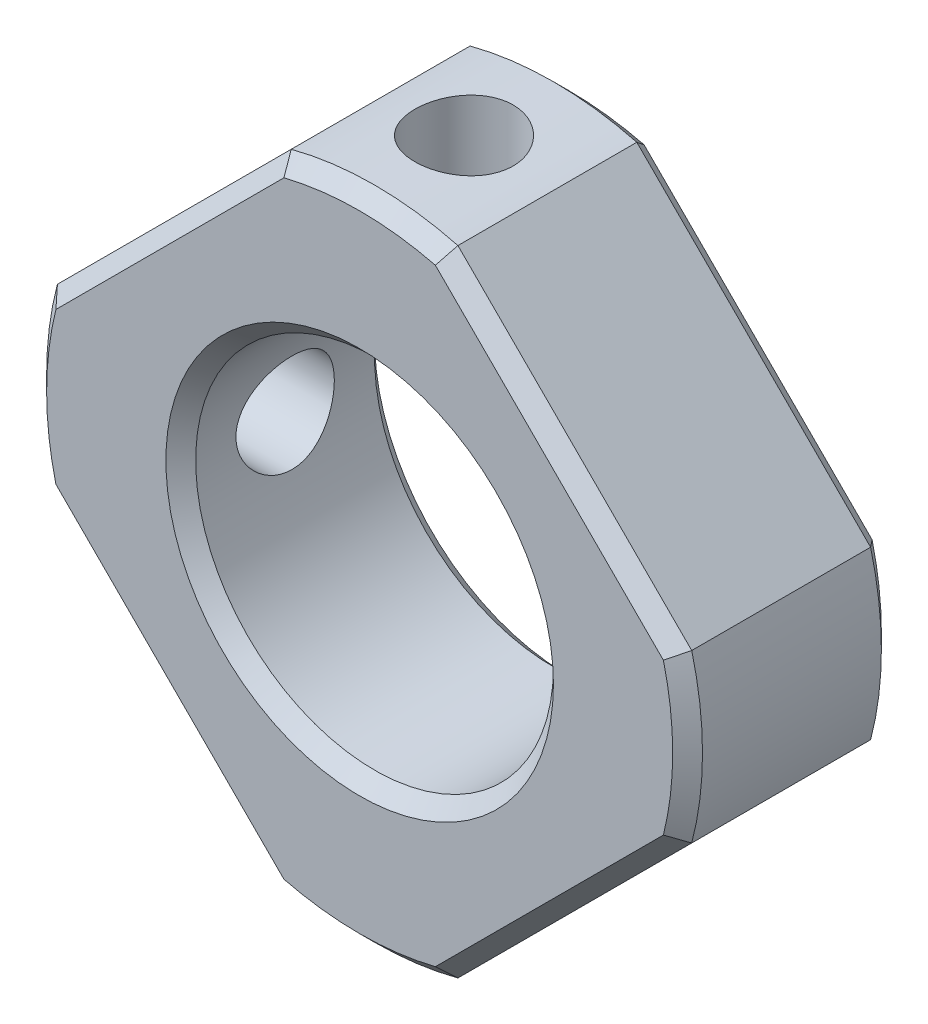
SolidWorks part; units mm, degrees
ref_plane "Front Plane" through (0, 0, 0) normal (0, 0, 1) x (1, 0, 0)
ref_plane "Top Plane" through (0, 0, 0) normal (0, 1, 0) x (1, 0, 0)
ref_plane "Right Plane" through (0, 0, 0) normal (1, 0, 0) x (0, 0, -1)
sketch "Sketch1" plane through (0, 0, 0) normal (0, 0, 1) x (1, 0, 0)
  line L1 (0, -13.435) -> (-13.435, 0)
  line L2 (0, -13.435) -> (13.435, 0)
  line L3 (13.435, 0) -> (0, 13.435)
  line L4 (-13.435, 0) -> (0, 13.435)
  line L5 (0, -13.435) -> (0, 13.435) construction
  line L6 (13.435, 0) -> (-13.435, 0) construction
  circle A0 centre (0, 0) radius 6
  point P0 (0, 0)
  dimension "D2" = 12
  dimension "D1" = 19
extrude "Boss-Extrude1" add sketch "Sketch1" along normal mid plane 7
sketch "Sketch2" plane through (0, 0, 3.5) normal (0, 0, 1) x (1, 0, 0)
  circle A0 centre (0, 0) radius 11
  dimension "D1" = 22
extrude "Cut-Extrude1" cut sketch "Sketch2" against normal through all flip side to cut
sketch "Sketch4" plane through (0, 0, 0) normal (0, 1, 0) x (1, 0, 0)
  circle A0 centre (0, 0) radius 1.65
  dimension "D1" = 3.3
extrude "Cut-Extrude2" cut sketch "Sketch4" along normal through all
sketch "Sketch5" plane through (0, 0, 0) normal (1, 0, 0) x (0, 0, -1)
  circle A0 centre (0, 0) radius 1.65
  dimension "D1" = 3.3
extrude "Cut-Extrude3" cut sketch "Sketch5" against normal through all
chamfer "Chamfer1" distance 0.5 angle 45 18 edges at (-6.7175, 6.7175, -3.5) (-11, 0, -3.5) (-6.7175, -6.7175, -3.5) (0, -11, -3.5) (6.7175, -6.7175, -3.5) (11, 0, -3.5) (6.7175, 6.7175, -3.5) (0, 11, -3.5) (6, 0, -3.5) (11, 0, 3.5) (6.7175, -6.7175, 3.5) (0, -11, 3.5) (-6.7175, -6.7175, 3.5) (-11, 0, 3.5) (-6.7175, 6.7175, 3.5) (0, 11, 3.5) (6.7175, 6.7175, 3.5) (6, 0, 3.5)
